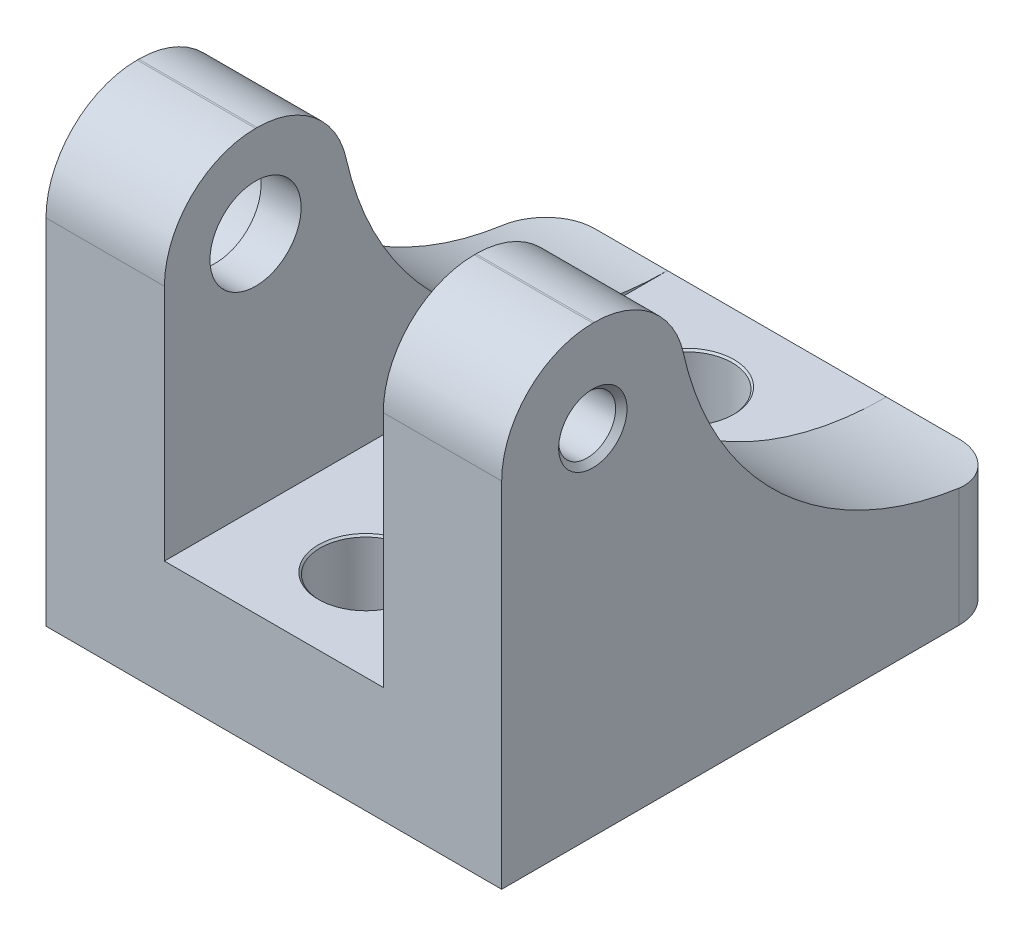
SolidWorks part; units mm, degrees
material "6061 Alloy"
ref_plane "Front Plane" through (0, 0, 0) normal (0, 0, 1) x (1, 0, 0)
ref_plane "Top Plane" through (0, 0, 0) normal (0, 1, 0) x (1, 0, 0)
ref_plane "Right Plane" through (0, 0, 0) normal (1, 0, 0) x (0, 0, -1)
sketch "Sketch1" plane through (0, 0, 0) normal (0, 1, 0) x (1, 0, 0)
  line L1 (0, 0) -> (63.5, 0)
  line L2 (0, 0) -> (0, 70.104)
  line L3 (0, 70.104) -> (63.5, 70.104)
  line L4 (63.5, 0) -> (63.5, 70.104)
  dimension "D1" = 70.104
  dimension "D2" = 63.5
extrude "Boss-Extrude1" add sketch "Sketch1" along normal blind 61.976
sketch "Sketch2" plane through (63.5, 0, 0) normal (1, 0, 0) x (0, 0, -1)
  circle A0 centre (70.104, 61.976) radius 45.8659
extrude "Cut-Extrude1" cut sketch "Sketch2" against normal blind 63.5
fillet "Fillet2" radius 12.7 2 edges at (31.75, 61.976, -24.2381) (31.75, 61.976, 0)
sketch "Sketch3" plane through (0, 0, -70.104) normal (0, 0, -1) x (-1, 0, 0)
  line L1 (-46.228, 63.5) -> (-17.272, 63.5)
  line L2 (-46.228, 63.5) -> (-46.228, 16.1101)
  line L3 (-46.228, 16.1101) -> (-17.272, 16.1101)
  line L4 (-17.272, 63.5) -> (-17.272, 16.1101)
  line L5 (-63.5, 52.03) -> (-63.5, 16.1101) construction
  line L6 (0, 16.1101) -> (-63.5, 16.1101) construction
  dimension "D1" = 28.956
  dimension "D2" = 17.272
extrude "Cut-Extrude2" cut sketch "Sketch3" against normal through all
sketch "Sketch4" plane through (0, 16.1101, 0) normal (0, 1, 0) x (1, 0, 0)
  line L0 (0, 70.104) -> (17.272, 70.104) construction
  line L1 (46.228, 0) -> (17.272, 0) construction
  circle A0 centre (31.8648, 57.404) radius 6.35
  circle A1 centre (31.8648, 12.6995) radius 6.35
  point P8 (31.75, 0)
  dimension "D2" = 12.7
  dimension "D3" = 12.7
  dimension "D1" = 12.7
  dimension "D4" = 12.7
extrude "Cut-Extrude3" cut sketch "Sketch4" against normal through all
chamfer "Chamfer1" distance 0.254 angle 45 2 edges at (31.8648, 16.1101, -6.3495) (31.8648, 16.1101, -51.054)
fillet "Fillet4" radius 6.35 2 edges at (0, 8.0551, -70.104) (63.5, 8.0551, -70.104)
sketch "Sketch5" plane through (0, 0, 0) normal (-1, 0, 0) x (0, 0, 1)
  circle A0 centre (-12.7, 49.276) radius 10.414
  dimension "D1" = 20.828
extrude "Cut-Extrude4" cut sketch "Sketch5" against normal blind 10.922
sketch "Sketch6" plane through (10.922, 0, 0) normal (-1, 0, 0) x (0, 0, 1)
  circle A0 centre (-12.7, 49.276) radius 6.35
  dimension "D1" = 12.7
extrude "Cut-Extrude5" cut sketch "Sketch6" against normal up to next
hole_wizard "3/8-16 Tapped Hole1" positions "Sketch7" profile "Sketch8" tap size "3/8-16" standard "ANSI Inch" end condition up to next
sketch "Sketch7" plane through (63.5, 0, 0) normal (1, 0, 0) x (0, 0, -1)
  point P0 (12.7, 49.276)
sketch "Sketch8" plane through (63.5, 49.276, -12.7) normal (0, 1, 0) x (0, 0, -1)
  line L0 (0, 0) -> (0, 17.272)
  line L1 (0, 17.272) -> (3.9687, 17.272)
  line L2 (3.9687, 17.272) -> (3.9687, 0.7938)
  line L3 (3.9687, 0.7938) -> (4.7625, 0)
  line L5 (4.7625, 0) -> (0, 0)
  line L6 (-3.9687, 0.7938) -> (-4.7625, 0) construction
  line L11 (0, -6.35) -> (0, 107.95) construction
  dimension "Thru Tap Drill Dia." = 7.9375
  dimension "Thru Tap Drill Depth" = 17.272
  dimension "Near C'Sink Dia." = 9.525
  dimension "Near C'Sink Angle" = 90
cosmetic thread "Hole Thread1" parameters "D2"=9.525
sketch "Sketch9" plane through (0, 0, 0) normal (0, 0, 1) x (1, 0, 0)
  line L1 (16.5, 16.1101) -> (47, 16.1101)
  line L2 (16.5, 16.1101) -> (16.5, 61.976)
  line L3 (16.5, 61.976) -> (47, 61.976)
  line L4 (47, 16.1101) -> (47, 61.976)
  line L5 (0, 61.976) -> (17.272, 61.976) construction
  line L6 (46.228, 16.1101) -> (17.272, 16.1101) construction
  line L8 (16.5, 16.1101) -> (0, 16.1101) construction
  line L9 (0, 49.276) -> (0, 0) construction
  line L10 (47, 16.1101) -> (63.5, 16.1101) construction
  line L11 (63.5, 49.276) -> (63.5, 0) construction
  dimension "D1" = 30.5
extrude "Cut-Extrude6" cut sketch "Sketch9" against normal through all
